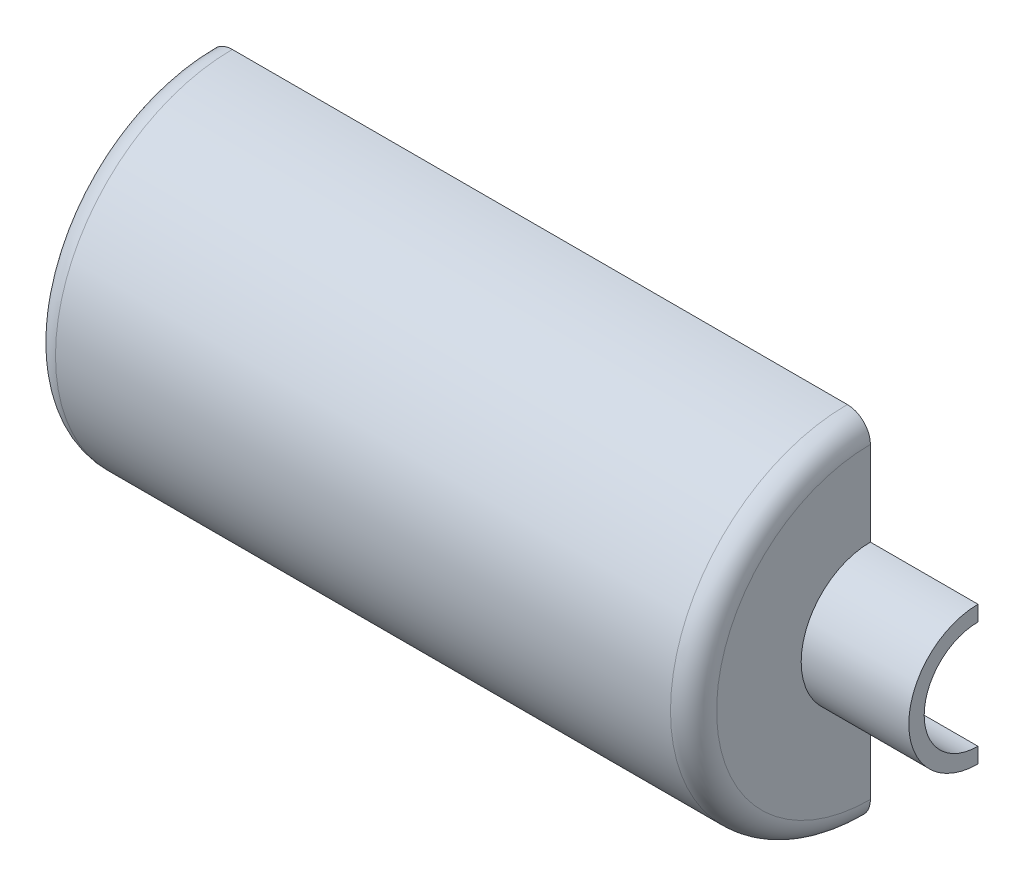
SolidWorks part; units mm, degrees
ref_plane "Front" through (0, 0, 0) normal (0, 0, 1) x (1, 0, 0)
ref_plane "Top" through (0, 0, 0) normal (0, 1, 0) x (1, 0, 0)
ref_plane "Right" through (0, 0, 0) normal (1, 0, 0) x (0, 0, -1)
sketch "Sketch1" plane through (0, 0, 0) normal (0, 0, 1) x (1, 0, 0)
  line L0 (0, 0) -> (92.5762, 0) construction
  line L1 (-215, 0) -> (-215, 100)
  line L2 (-200, 115) -> (200, 115)
  line L3 (215, 100) -> (215, 45)
  line L4 (215, 45) -> (285, 45)
  line L5 (-200, 0) -> (-200, 92.5)
  line L6 (-192.5, 100) -> (192.5, 100)
  line L7 (200, 92.5) -> (200, 35)
  line L8 (200, 35) -> (285, 35)
  line L9 (200, 30) -> (285, 30) construction
  line L10 (200, 100) -> (200, 30) construction
  line L11 (285, 35) -> (285, 45)
  line L12 (-215, 0) -> (-200, 0)
  line L13 (-200, 100) -> (200, 100) construction
  line L14 (-200, 0) -> (-200, 100) construction
  line L15 (-215, 0) -> (-215, 115) construction
  line L16 (-215, 115) -> (215, 115) construction
  line L17 (215, 115) -> (215, 45) construction
  arc A0 (-192.5, 100) -> (-200, 92.5) centre (-192.5, 92.5) ccw
  arc A1 (200, 92.5) -> (192.5, 100) centre (192.5, 92.5) ccw
  arc A2 (-215, 100) -> (-200, 115) centre (-200, 100) cw
  arc A3 (215, 100) -> (200, 115) centre (200, 100) ccw
  dimension "D8" = 7.5
  dimension "D9" = 7.5
  dimension "D10" = 15
  dimension "D11" = 15
  dimension "D1" = 215
  dimension "D2" = 500
  dimension "D3" = 70
  dimension "D4" = 230
  dimension "D5" = 90
  dimension "D7" = 10
  dimension "D12" = 15
  dimension "D6" = 15
revolve "Revolve1" add sketch "Sketch1" angle 180 about L0
